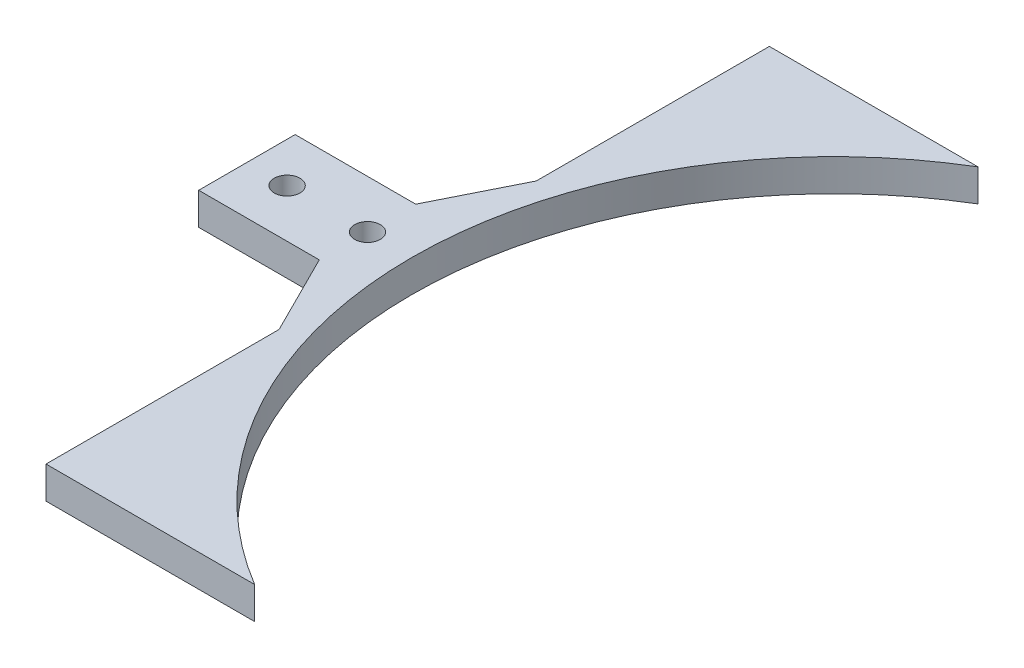
SolidWorks part; units mm, degrees
ref_plane "前视基准面" through (0, 0, 0) normal (0, 0, 1) x (1, 0, 0)
ref_plane "上视基准面" through (0, 0, 0) normal (0, 1, 0) x (1, 0, 0)
ref_plane "右视基准面" through (0, 0, 0) normal (1, 0, 0) x (0, 0, -1)
sketch "草图2" plane through (0, 0, 0) normal (0, 1, 0) x (1, 0, 0)
  line L0 (31.7351, 1.8093) -> (-68.9587, 1.8093) construction
  line L1 (-21.2649, 46.8093) -> (4.6935, 46.8093)
  line L2 (-21.2649, -43.1907) -> (4.6935, -43.1907)
  line L3 (-21.2649, 46.8093) -> (-21.2649, 17.8093)
  line L4 (-41.2649, 7.8093) -> (-26.2649, 7.8093)
  line L5 (-41.2649, -4.1907) -> (-26.2649, -4.1907)
  line L6 (-41.2649, 7.8093) -> (-41.2649, -4.1907)
  line L7 (-21.2649, -14.1907) -> (-21.2649, -43.1907)
  line L8 (-26.2649, 7.8093) -> (-21.2649, 17.8093)
  line L9 (-26.2649, -4.1907) -> (-21.2649, -14.1907)
  arc A0 (4.6935, 46.8093) -> (4.6935, -43.1907) centre (31.7351, 1.8093) ccw
  circle A1 centre (-36.2649, 1.8093) radius 1.6
  circle A2 centre (-26.2649, 1.8093) radius 1.6
  point P2 (-20.7649, 1.8093)
  dimension "D1" = 105
  dimension "D4" = 6
  dimension "D6" = 10
  dimension "D2" = 45
  dimension "D3" = 53
  dimension "D5" = 20
  dimension "D7" = 5
  dimension "D8" = 10
  dimension "D9" = 5
extrude "凸台-拉伸1" add sketch "草图2" along normal blind 4
